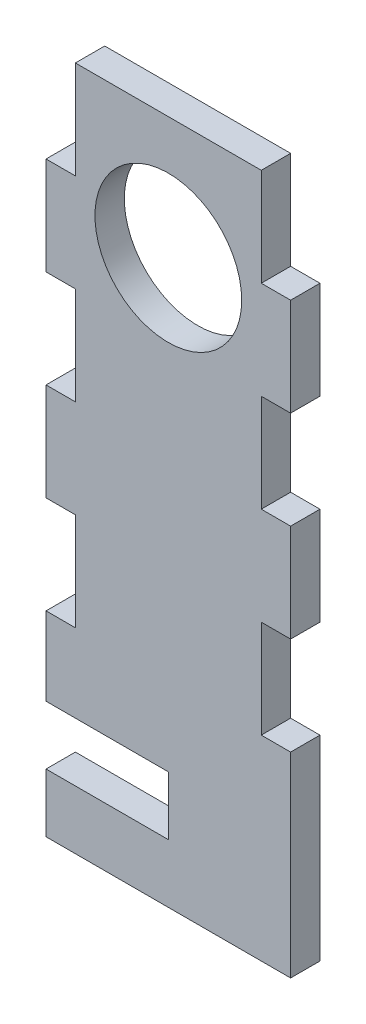
SolidWorks part; units mm, degrees
material "PC High Viscosity"
ref_plane "Front Plane" through (0, 0, 0) normal (0, 0, 1) x (1, 0, 0)
ref_plane "Top Plane" through (0, 0, 0) normal (0, 1, 0) x (1, 0, 0)
ref_plane "Right Plane" through (0, 0, 0) normal (1, 0, 0) x (0, 0, -1)
sketch "Sketch1" plane through (0, 0, 0) normal (0, 0, 1) x (1, 0, 0)
  line L1 (-12.5, -35) -> (12.5, -35)
  line L2 (-12.5, -35) -> (-12.5, 35)
  line L3 (-12.5, 35) -> (12.5, 35)
  line L4 (12.5, -35) -> (12.5, 35)
  line L5 (-12.5, -35) -> (12.5, 35) construction
  line L6 (-12.5, 35) -> (12.5, -35) construction
  point P0 (0, 0)
  dimension "D1" = 70
  dimension "D2" = 25
extrude "Boss-Extrude1" add sketch "Sketch1" along normal blind 3 contours L3 L4 L1 L2
sketch "Sketch2" plane through (0, 0, 3) normal (0, 0, 1) x (1, 0, 0)
  line L0 (-9.5, -5) -> (-9.5, -15)
  line L1 (12.5, 35) -> (9.5, 35)
  line L2 (12.5, 35) -> (12.5, 25)
  line L3 (12.5, 25) -> (9.5, 25)
  line L4 (9.5, 35) -> (9.5, 25)
  line L5 (12.5, -35) -> (12.5, 35) construction
  line L6 (12.5, 15) -> (9.5, 15)
  line L7 (12.5, 15) -> (12.5, 5)
  line L8 (12.5, 5) -> (9.5, 5)
  line L9 (0, -15) -> (0, 35) construction
  line L10 (9.5, 15) -> (9.5, 5)
  line L11 (12.5, -5) -> (12.5, 5) construction
  line L12 (12.5, -5) -> (9.5, -5)
  line L13 (12.5, -5) -> (12.5, -15)
  line L14 (12.5, -15) -> (9.5, -15)
  line L15 (9.5, -5) -> (9.5, -15)
  line L16 (12.5, 15) -> (12.5, 25) construction
  line L17 (-12.5, -15) -> (-9.5, -15)
  line L18 (-12.5, -5) -> (-12.5, -15)
  line L19 (-12.5, -5) -> (-9.5, -5)
  line L20 (-9.5, 15) -> (-9.5, 5)
  line L21 (-12.5, 5) -> (-9.5, 5)
  line L22 (-12.5, 15) -> (-12.5, 5)
  line L23 (-12.5, 15) -> (-9.5, 15)
  line L24 (-9.5, 35) -> (-9.5, 25)
  line L25 (-12.5, 25) -> (-9.5, 25)
  line L26 (-12.5, 35) -> (-12.5, 25)
  line L27 (-12.5, 35) -> (-9.5, 35)
  line L28 (-12.5, 35) -> (-12.5, -35) construction
  line L30 (-12.5, -35) -> (12.5, -35) construction
  line L31 (-12.5, -23) -> (0, -23)
  line L32 (-12.5, -23) -> (-12.5, -29)
  line L33 (-12.5, -29) -> (0, -29)
  line L34 (0, -23) -> (0, -29)
  line L36 (0, 22.5) -> (-12.5, 22.5) construction
  line L37 (0, 22.5) -> (0, 35) construction
  line L38 (0, 35) -> (-12.5, 35) construction
  line L39 (-12.5, 22.5) -> (-12.5, 35) construction
  circle A0 centre (0, 22.5) radius 7.5
  dimension "D4" = 15
  dimension "D1" = 10
  dimension "D2" = 3
  dimension "D5" = 6
  dimension "D6" = 6
extrude "Cut-Extrude1" cut sketch "Sketch2" against normal blind 3
equation "\"pulley_pitch_diam\"= 12.73mm"
equation "\"pulley_total_width\"= 16mm"
equation "\"pulley_total_diam\"= 16mm"
equation "\"belt_width\"= 6mm"
equation "\"material_thickness\"= 3mm"
equation "\"shaft_diam\"= 8mm"
equation "\"bearing_od\"= 22mm"
equation "\"bearing_thickness\"= 7mm"
equation "\"D1@Boss-Extrude1\"=\"material_thickness\""
equation "\"D2@Sketch2\"=\"material_thickness\""
